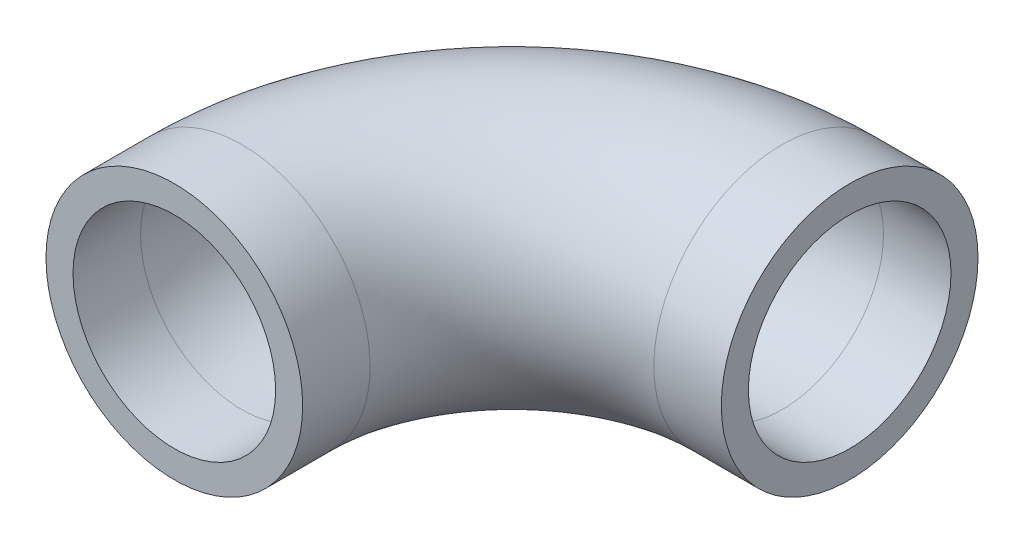
SolidWorks part; units mm, degrees
material "PVC Rigid"
ref_plane "Front Plane" through (0, 0, 0) normal (0, 0, 1) x (1, 0, 0)
ref_plane "Top Plane" through (0, 0, 0) normal (0, 1, 0) x (1, 0, 0)
ref_plane "Right Plane" through (0, 0, 0) normal (1, 0, 0) x (0, 0, -1)
sketch "Sketch1" plane through (0, 0, 0) normal (0, 0, 1) x (1, 0, 0)
  circle A0 centre (0, 0) radius 24.13
  circle A1 centre (0, 0) radius 19.05
  dimension "D1" = 48.26
  dimension "D2" = 38.1
sketch "Sketch15" plane through (0, 0, 0) normal (0, 1, 0) x (1, 0, 0)
  line L0 (0, 0) -> (0, 12.7)
  line L1 (50.8, 63.5) -> (63.5, 63.5)
  arc A0 (0, 12.7) -> (50.8, 63.5) centre (50.8, 12.7) cw
  dimension "D2" = 50.8
  dimension "D1" = 12.7
sweep "Sweep1" add profiles "Sketch1" path "Sketch15"
